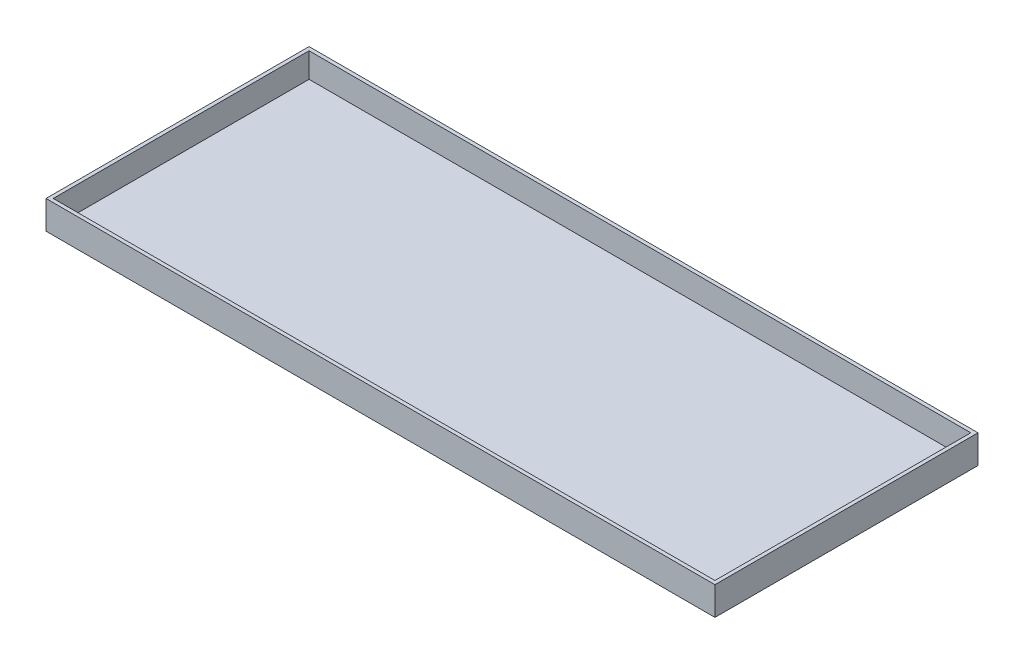
SolidWorks part; units mm, degrees
ref_plane "Front Plane" through (0, 0, 0) normal (0, 0, 1) x (1, 0, 0)
ref_plane "Top Plane" through (0, 0, 0) normal (0, 1, 0) x (1, 0, 0)
ref_plane "Right Plane" through (0, 0, 0) normal (1, 0, 0) x (0, 0, -1)
sketch "Sketch1" plane through (0, 0, 0) normal (0, 1, 0) x (1, 0, 0)
  line L1 (-35.3314, 13.8938) -> (35.3314, 13.8938)
  line L2 (-35.3314, 13.8938) -> (-35.3314, -13.8938)
  line L3 (-35.3314, -13.8938) -> (35.3314, -13.8938)
  line L4 (35.3314, 13.8938) -> (35.3314, -13.8938)
  line L5 (-35.3314, 13.8938) -> (35.3314, -13.8938) construction
  line L6 (-35.3314, -13.8938) -> (35.3314, 13.8938) construction
  point P0 (0, 0)
  dimension "D1" = 70.6628
  dimension "D2" = 27.7876
extrude "Boss-Extrude1" add sketch "Sketch1" along normal blind 2.9972
shell "Shell1" thickness 0.381
